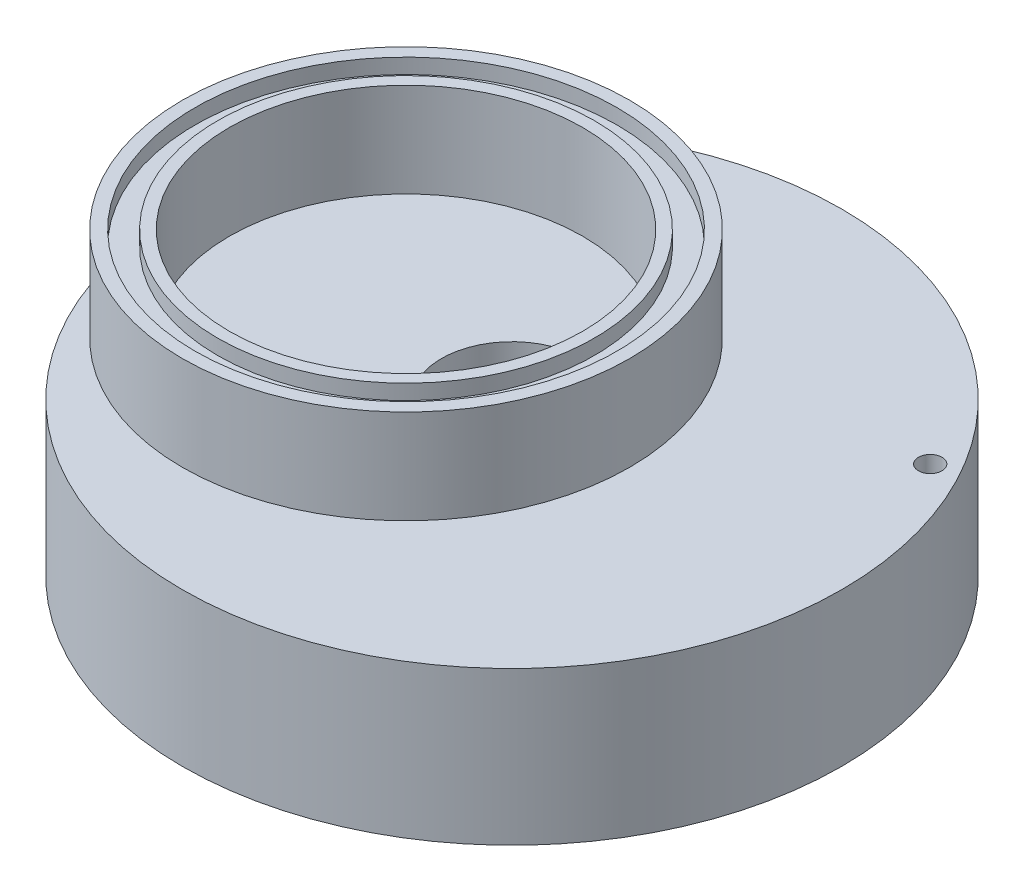
SolidWorks part; units mm, degrees
ref_plane "Front Plane" through (0, 0, 0) normal (0, 0, 1) x (1, 0, 0)
ref_plane "Top Plane" through (0, 0, 0) normal (0, 1, 0) x (1, 0, 0)
ref_plane "Right Plane" through (0, 0, 0) normal (1, 0, 0) x (0, 0, -1)
sketch "Sketch1" plane through (0, 0, 0) normal (0, 0, 1) x (1, 0, 0)
  line L0 (0, 0) -> (0, 16.7409) construction
  line L1 (-9.525, -6.35) -> (-9.525, 0)
  line L2 (-9.525, 0) -> (-44.45, 0)
  line L3 (-44.45, 0) -> (-44.45, -20.6375)
  line L4 (-33.3375, -20.6375) -> (-31.75, -20.6375)
  line L5 (-31.75, -20.6375) -> (-31.75, -19.05)
  line L6 (-31.75, -19.05) -> (-15.875, -6.35)
  line L7 (-44.45, -20.6375) -> (-36.3855, -20.6375)
  line L8 (-36.3855, -20.6375) -> (-36.3855, -18.6055)
  line L9 (-36.3855, -18.6055) -> (-33.3375, -18.6055)
  line L10 (-33.3375, -18.6055) -> (-33.3375, -20.6375)
  line L11 (-9.525, -6.35) -> (-15.875, -6.35)
  dimension "D1" = 6.35
  dimension "D2" = 9.525
  dimension "D3" = 1.5875
  dimension "D4" = 31.75
  dimension "D5" = 1.5875
  dimension "D6" = 12.7
  dimension "D7" = 20.6375
  dimension "D8" = 3.048
  dimension "D9" = 2.032
  dimension "D10" = 44.45
  dimension "D11" = 6.35
revolve "Revolve1" add sketch "Sketch1" angle 360 about L0
sketch "Sketch2" plane through (0, 0, 0) normal (0, 1, 0) x (1, 0, 0)
  circle A0 centre (-14.2875, 0) radius 30.1625
  circle A1 centre (-14.2875, 0) radius 23.8125
  circle A2 centre (0, 0) radius 44.45 construction
  circle A3 centre (0, 0) radius 9.525 construction
  point P3 (-13.6947, 2.2218)
  point P4 (0, 0)
  point P5 (-11.6551, 1.2748)
  point P6 (0, 0)
  dimension "D1" = 6.35
extrude "Boss-Extrude1" add sketch "Sketch2" along normal blind 12.7
sketch "Sketch4" plane through (0, 12.7, 0) normal (0, 1, 0) x (1, 0, 0)
  circle A0 centre (-14.2875, 0) radius 25.4
  circle A1 centre (-14.2875, 0) radius 28.448
  circle A2 centre (-14.2875, 0) radius 23.8125 construction
  circle A3 centre (-14.2875, 0) radius 23.8125 construction
  dimension "D1" = 3.048
  dimension "D2" = 1.5875
extrude "Cut-Extrude1" cut sketch "Sketch4" against normal blind 2.032
hole_wizard "1/8 (0.125) Diameter Hole1" positions "Sketch7" profile "Sketch8" hole size "1/8" standard "ANSI Inch"
sketch "Sketch7" plane through (0, -20.6375, 0) normal (0, -1, 0) x (-1, 0, 0)
  point P0 (-41.275, 0)
  dimension "D1" = 41.275
sketch "Sketch8" plane through (41.275, -20.6375, 0) normal (1, 0, 0) x (0, 0, -1)
  line L0 (0, 0) -> (0, 7.3039)
  line L1 (0, 7.3039) -> (1.5875, 6.35)
  line L2 (1.5875, 6.35) -> (1.5875, 0)
  line L5 (1.5875, 0) -> (0, 0)
  line L10 (0, 7.3039) -> (-1.5875, 6.35) construction
  line L11 (0, -6.35) -> (0, 107.95) construction
  dimension "Hole Dia." = 3.175
  dimension "Hole Depth" = 6.35
  dimension "Drill Angle" = 118
hole_wizard "1/8 (0.125) Diameter Hole2" positions "Sketch9" profile "Sketch10" hole size "1/8" standard "ANSI Inch"
sketch "Sketch9" plane through (0, 0, 0) normal (0, 1, 0) x (1, 0, 0)
  line L0 (0, 0) -> (35.3538, 0) construction
  line L2 (0, 0) -> (35.7452, 20.6375) construction
  point P0 (35.7452, 20.6375)
  dimension "D1" = 41.275
  dimension "D2" = 30
sketch "Sketch10" plane through (35.7452, 0, -20.6375) normal (1, 0, 0) x (0, 0, 1)
  line L0 (0, 0) -> (0, 7.3039)
  line L1 (0, 7.3039) -> (1.5875, 6.35)
  line L2 (1.5875, 6.35) -> (1.5875, 0)
  line L5 (1.5875, 0) -> (0, 0)
  line L10 (0, 7.3039) -> (-1.5875, 6.35) construction
  line L11 (0, -6.35) -> (0, 107.95) construction
  dimension "Hole Dia." = 3.175
  dimension "Hole Depth" = 6.35
  dimension "Drill Angle" = 118
